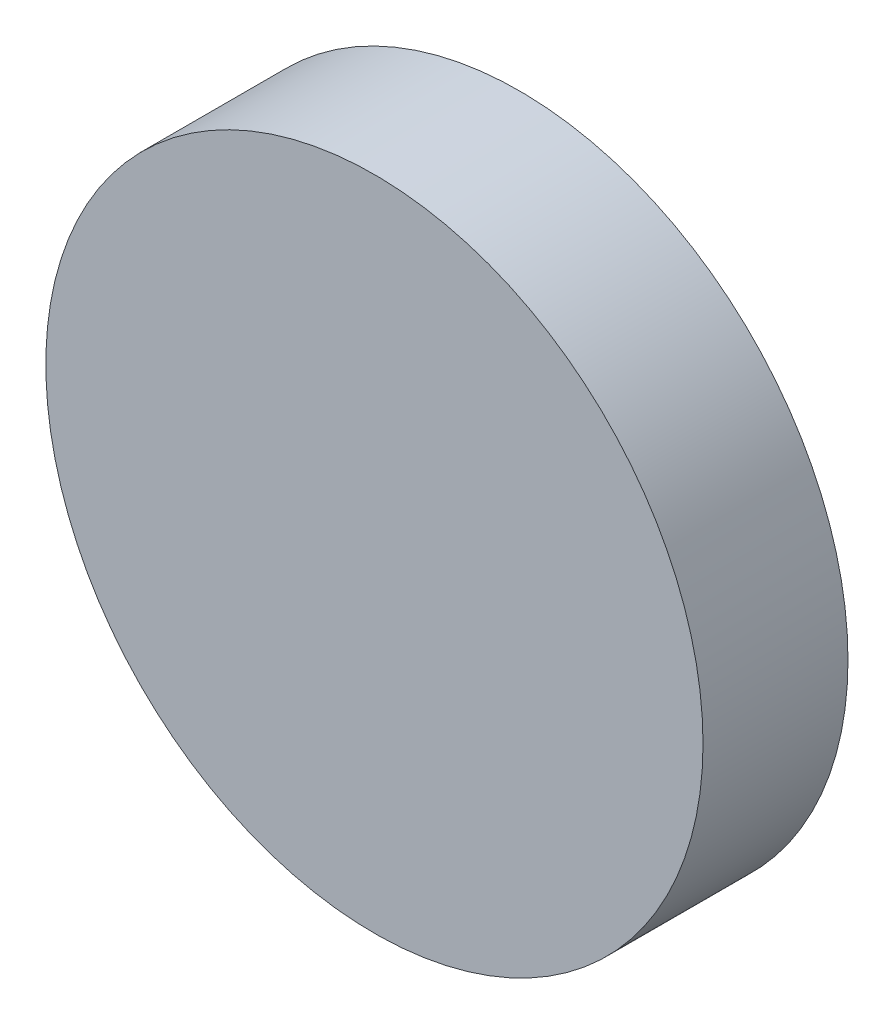
SolidWorks part; units mm, degrees
material "0.6010 (EN-GJL-100)"
ref_plane "Alzado" through (0, 0, 0) normal (0, 0, 1) x (1, 0, 0)
ref_plane "Planta" through (0, 0, 0) normal (0, 1, 0) x (1, 0, 0)
ref_plane "Vista lateral" through (0, 0, 0) normal (1, 0, 0) x (0, 0, -1)
sketch "Croquis1" plane through (0, 0, 0) normal (0, 0, 1) x (1, 0, 0)
  circle A0 centre (0, 0) radius 2.04
  dimension "D1" = 4.08
extrude "Saliente-Extruir1" add sketch "Croquis1" along normal blind 0.9
